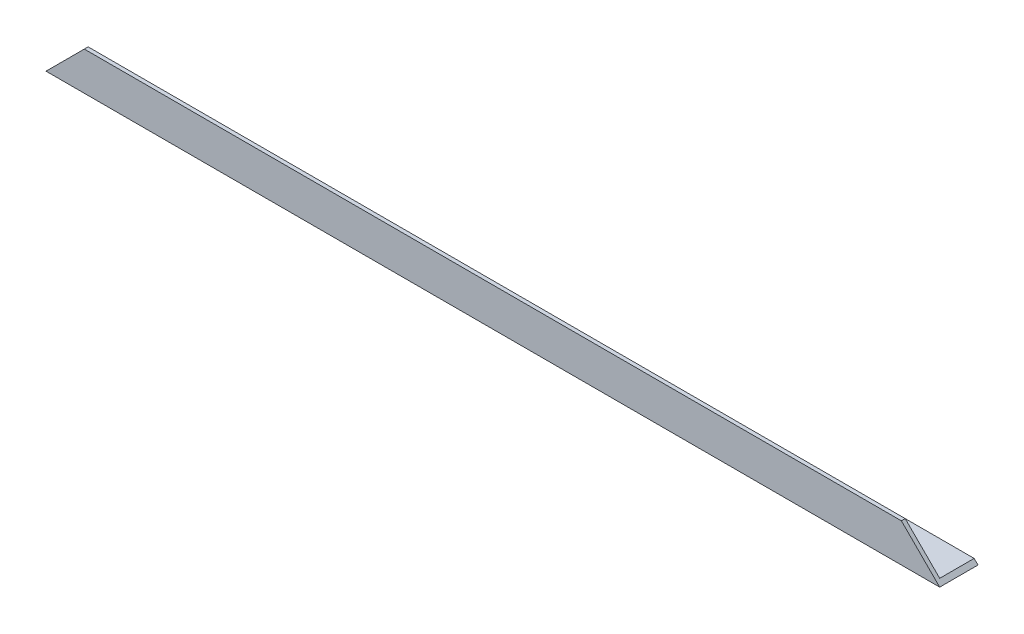
SolidWorks part; units mm, degrees
ref_plane "Спереди" through (0, 0, 0) normal (0, 0, 1) x (1, 0, 0)
ref_plane "Сверху" through (0, 0, 0) normal (0, 1, 0) x (1, 0, 0)
ref_plane "Справа" through (0, 0, 0) normal (1, 0, 0) x (0, 0, -1)
sketch "Эскиз1" plane through (0, 0, 0) normal (1, 0, 0) x (0, 0, -1)
  line L0 (0, 0) -> (0, 15)
  line L1 (0, 15) -> (1.5, 15)
  line L2 (1.5, 15) -> (1.5, 1.5)
  line L3 (1.5, 1.5) -> (15, 1.5)
  line L4 (15, 1.5) -> (15, 0)
  line L5 (15, 0) -> (0, 0)
  dimension "D1" = 15
  dimension "D2" = 15
  dimension "D3" = 1.5
  dimension "D4" = 1.5
extrude "Бобышка-Вытянуть1" add sketch "Эскиз1" along normal blind 350
ref_plane "Плоскость1" through (175, 0, 0) normal (-1, 0, 0) x (0, 0, 1)
sketch "Эскиз2" plane through (0, 0, 0) normal (0, 0, 1) x (1, 0, 0)
  line L0 (0, 0) -> (21.7299, 21.7299)
  line L1 (21.7299, 21.7299) -> (0, 21.7299)
  line L2 (0, 21.7299) -> (0, 0)
  dimension "D1" = 45
extrude "Вырез-Вытянуть1" cut sketch "Эскиз2" against normal through all
mirror "Зеркальное отражение1" about plane through (175, 0, 0) normal (-1, 0, 0) of "Вырез-Вытянуть1"
